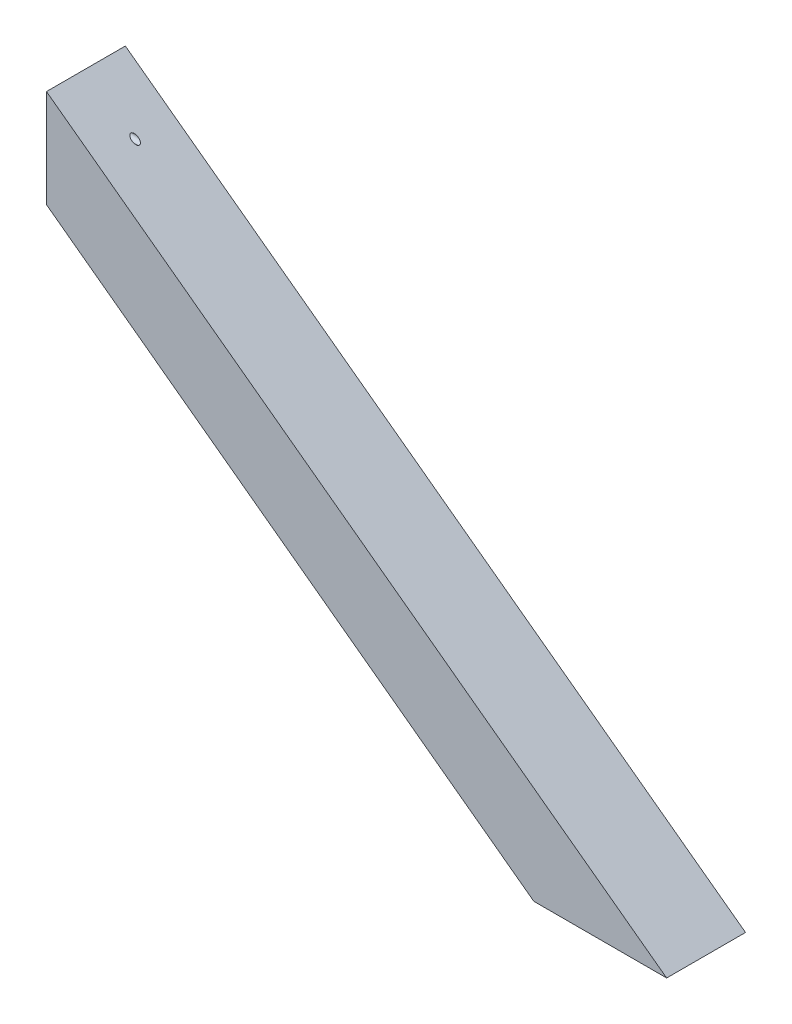
SolidWorks part; units mm, degrees
material "Pin"
ref_plane "Plan de face" through (0, 0, 0) normal (0, 0, 1) x (1, 0, 0)
ref_plane "Plan de dessus" through (0, 0, 0) normal (0, 1, 0) x (1, 0, 0)
ref_plane "Plan de droite" through (0, 0, 0) normal (1, 0, 0) x (0, 0, -1)
sketch "Esquisse1" plane through (0, 0, 0) normal (0, 0, 1) x (1, 0, 0)
  line L0 (-141.6092, -140.0916) -> (174.2853, -140.0916) construction
  line L1 (-97.6092, 115.2199) -> (-97.6092, 60.5378)
  line L2 (248.3908, -140.0916) -> (-97.6092, 115.2199)
  line L3 (174.2853, -140.0916) -> (-97.6092, 60.5378)
  line L5 (248.3908, -140.0916) -> (174.2853, -140.0916)
  line L6 (174.2853, -140.0916) -> (248.3908, -140.0916) construction
  dimension "D1" = 390
  dimension "D2" = 430
extrude "Boss.-Extru.1" add sketch "Esquisse1" along normal blind 44
sketch "Esquisse2" plane through (-97.6092, 0, 0) normal (-1, 0, 0) x (0, 0, 1)
  line L0 (0, 115.2199) -> (0, 60.5378) construction
  line L1 (44, 115.2199) -> (0, 115.2199) construction
  circle A0 centre (22, 94.9699) radius 1.75
  dimension "D2" = 3.5
  dimension "D3" = 20.25
  dimension "D1" = 22
extrude "Enlèv. mat.-Extru.1" cut sketch "Esquisse2" against normal up to surface (27.4429 mm away)
